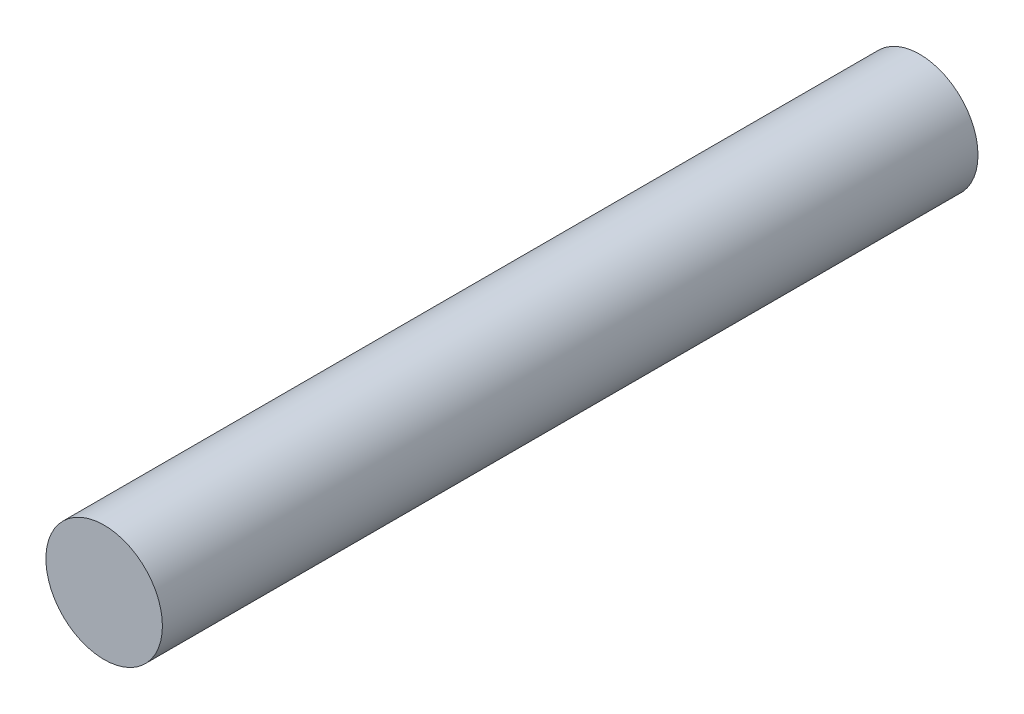
SolidWorks part; units mm, degrees
ref_plane "Front Plane" through (0, 0, 0) normal (0, 0, 1) x (1, 0, 0)
ref_plane "Top Plane" through (0, 0, 0) normal (0, 1, 0) x (1, 0, 0)
ref_plane "Right Plane" through (0, 0, 0) normal (1, 0, 0) x (0, 0, -1)
sketch "Sketch1" plane through (0, 0, 0) normal (0, 0, 1) x (1, 0, 0)
  circle A0 centre (0, 0) radius 1
  dimension "D1" = 2
extrude "Boss-Extrude1" add sketch "Sketch1" along normal mid plane 14
